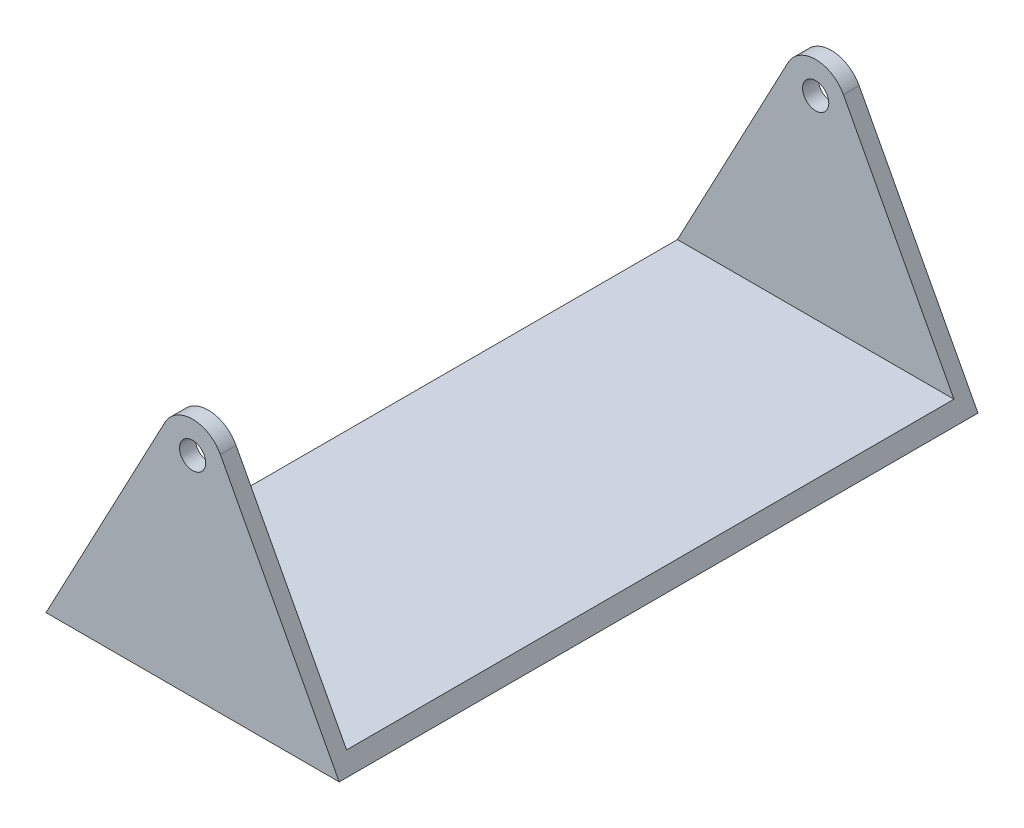
SolidWorks part; units mm, degrees
ref_plane "Plan de face" through (0, 0, 0) normal (0, 0, 1) x (1, 0, 0)
ref_plane "Plan de dessus" through (0, 0, 0) normal (0, 1, 0) x (1, 0, 0)
ref_plane "Plan de droite" through (0, 0, 0) normal (1, 0, 0) x (0, 0, -1)
sketch "Esquisse1" plane through (0, 0, 0) normal (0, 0, 1) x (1, 0, 0)
  line L0 (0, 0) -> (0, 51.1476) construction
  line L1 (-5.301, 42.8107) -> (-28, 0)
  line L4 (28, 0) -> (-28, 0)
  line L8 (5.301, 42.8107) -> (28, 0)
  arc A0 (5.301, 42.8107) -> (-5.301, 42.8107) centre (0, 40) ccw
  circle A1 centre (0, 40) radius 2.5
  point P3 (0, 18.3754)
  point P5 (0, 0)
  point P7 (0, 0)
  dimension "D3" = 12
  dimension "D4" = 5
  dimension "D1" = 56
  dimension "D5" = 40
extrude "Boss.-Extru.1" add sketch "Esquisse1" along normal mid plane 122
sketch "Esquisse2" plane through (0, 0, 0) normal (1, 0, 0) x (0, 0, -1)
  line L0 (0, 0) -> (0, 77.2093) construction
  line L1 (-61, 0) -> (61, 0) construction
  line L2 (58, 46) -> (-58, 46)
  line L3 (58, 46) -> (58, 3)
  line L4 (58, 3) -> (-58, 3)
  line L5 (-58, 46) -> (-58, 3)
  line L6 (58, 46) -> (-58, 3) construction
  line L7 (58, 3) -> (-58, 46) construction
  point P3 (0, 24.5)
  dimension "D1" = 3
  dimension "D2" = 116
extrude "Enlèv. mat.-Extru.1" cut sketch "Esquisse2" against normal through all and the other way through all
